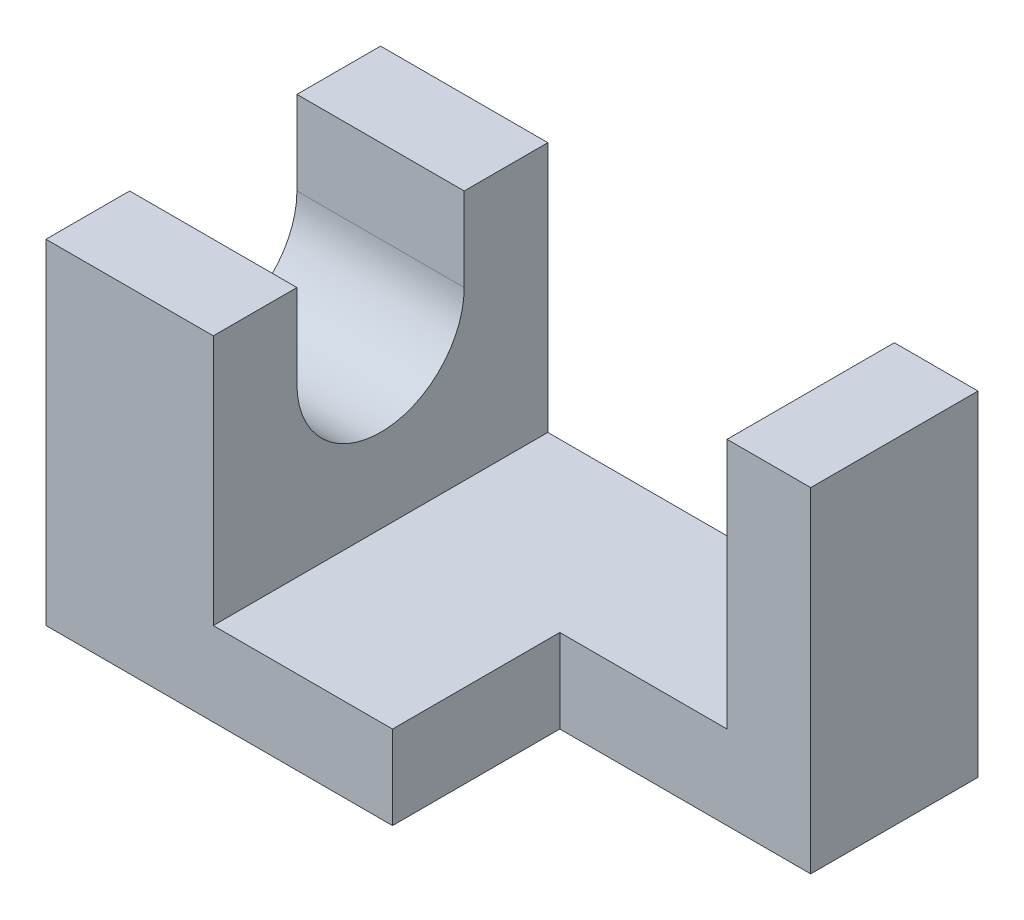
SolidWorks part; units mm, degrees
material "회주철"
ref_plane "정면" through (0, 0, 0) normal (0, 0, 1) x (1, 0, 0)
ref_plane "윗면" through (0, 0, 0) normal (0, 1, 0) x (1, 0, 0)
ref_plane "우측면" through (0, 0, 0) normal (1, 0, 0) x (0, 0, -1)
sketch "스케치1" plane through (0, 0, 0) normal (0, 0, 1) x (1, 0, 0)
  line L0 (0, 0) -> (0, 28)
  line L1 (0, 28) -> (14, 28)
  line L2 (0, 0) -> (50, 0)
  line L3 (50, 0) -> (50, 28)
  line L4 (50, 28) -> (43, 28)
  line L5 (14, 7) -> (43, 7)
  line L6 (14, 28) -> (14, 7)
  line L7 (43, 28) -> (43, 7)
  line L8 (0, 7) -> (50, 7) construction
  dimension "D1" = 14
  dimension "D2" = 43
  dimension "D3" = 50
  dimension "D4" = 28
  dimension "D5" = 7
extrude "보스-돌출1" add sketch "스케치1" along normal mid plane 28
sketch "스케치2" plane through (0, 0, 0) normal (0, 1, 0) x (1, 0, 0)
  line L0 (50, -14) -> (50, 0)
  line L1 (50, 0) -> (29, 0)
  line L2 (29, 0) -> (29, -14)
  line L3 (43, -14) -> (14, -14) construction
  line L4 (29, -14) -> (50, -14)
  dimension "D1" = 29
extrude "컷-돌출1" cut sketch "스케치2" along normal through all
sketch "스케치3" plane through (0, 0, 0) normal (1, 0, 0) x (0, 0, -1)
  line L1 (0, 28) -> (0, 0) construction
  line L2 (-7, 21) -> (-7, 28)
  line L3 (7, 21) -> (7, 28)
  line L4 (-7, 28) -> (7, 28)
  arc A0 (-7, 21) -> (7, 21) centre (0, 21) ccw
  dimension "D1" = 7
  dimension "D2" = 21
extrude "컷-돌출2" cut sketch "스케치3" along normal up to next
